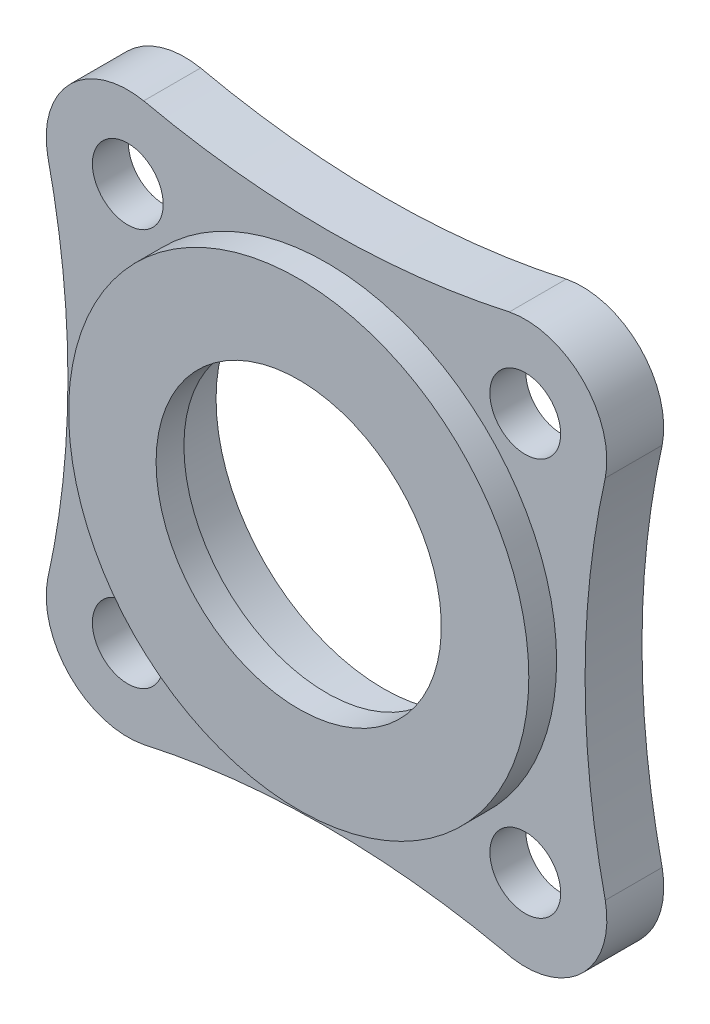
SolidWorks part; units mm, degrees
ref_plane "Front Plane" through (0, 0, 0) normal (0, 0, 1) x (1, 0, 0)
ref_plane "Top Plane" through (0, 0, 0) normal (0, 1, 0) x (1, 0, 0)
ref_plane "Right Plane" through (0, 0, 0) normal (1, 0, 0) x (0, 0, -1)
sketch "Sketch1" plane through (0, 0, 0) normal (0, 0, 1) x (1, 0, 0)
  circle A0 centre (0, 0) radius 16
  circle A1 centre (19, 19) radius 3.385
  circle A2 centre (-19, 19) radius 3.385
  circle A3 centre (-19, -19) radius 3.385
  circle A4 centre (19.0035, -19.0175) radius 3.385
  arc A5 (16.825, -26.5071) -> (26.65, -17.4774) centre (19.0035, -19.0175) ccw
  arc A6 (-26.6503, -17.4792) -> (-17.155, -26.5787) centre (-19, -19) ccw
  arc A7 (-17.1534, 26.5782) -> (-26.65, 17.4774) centre (-19, 19) ccw
  arc A8 (26.6503, 17.4792) -> (17.155, 26.5787) centre (19, 19) ccw
  arc A9 (-17.4792, 26.6503) -> (17.4774, 26.65) centre (-0.0002, 104.9224) ccw
  circle A10 centre (0, 0) radius 16
  arc A11 (26.6503, 17.4792) -> (26.65, -17.4774) centre (104.9224, 0.0002) ccw
  circle A12 centre (0, 0) radius 16
  arc A13 (17.4792, -26.6503) -> (-17.4774, -26.65) centre (0.0002, -104.9224) ccw
  circle A14 centre (0, 0) radius 16
  arc A15 (-26.6503, -17.4792) -> (-26.65, 17.4774) centre (-104.9224, -0.0002) ccw
  point P33 (0, 0)
  dimension "D1" = 32
  dimension "D4" = 6.77
  dimension "D5" = 6.77
  dimension "D6" = 6.77
  dimension "D7" = 6.77
  dimension "D8" = 15.6
  dimension "D9" = 15.6
  dimension "D10" = 15.6
  dimension "D11" = 15.6
  dimension "D12" = 80.2
  dimension "D2" = 38
  dimension "D3" = 38
  dimension "D13" = 4
extrude "Boss-Extrude1" add sketch "Sketch1" along normal blind 5.44
sketch "Sketch2" plane through (0, 0, 0) normal (0, 0, -1) x (-1, 0, 0)
  circle A0 centre (19, 19) radius 6.5
  circle A1 centre (-19, 19) radius 6.5
  circle A2 centre (-19.0035, -19.0175) radius 6.5
  circle A3 centre (19, -19) radius 6.5
  dimension "D1" = 13
  dimension "D2" = 13
  dimension "D3" = 13
  dimension "D4" = 13
extrude "Cut-Extrude1" cut sketch "Sketch2" against normal blind 2 contours A1 | A0 | A2 | A3
sketch "Sketch3" plane through (0, 0, 5.44) normal (0, 0, 1) x (1, 0, 0)
  circle A0 centre (0, 0) radius 22
  dimension "D1" = 44
extrude "Boss-Extrude2" add sketch "Sketch3" along normal blind 2.66
sketch "Sketch4" plane through (0, 0, 5.44) normal (0, 0, -1) x (-1, 0, 0)
  circle A0 centre (0, 0) radius 13.635
  dimension "D1" = 27.27
extrude "Cut-Extrude2" cut sketch "Sketch4" against normal through all
